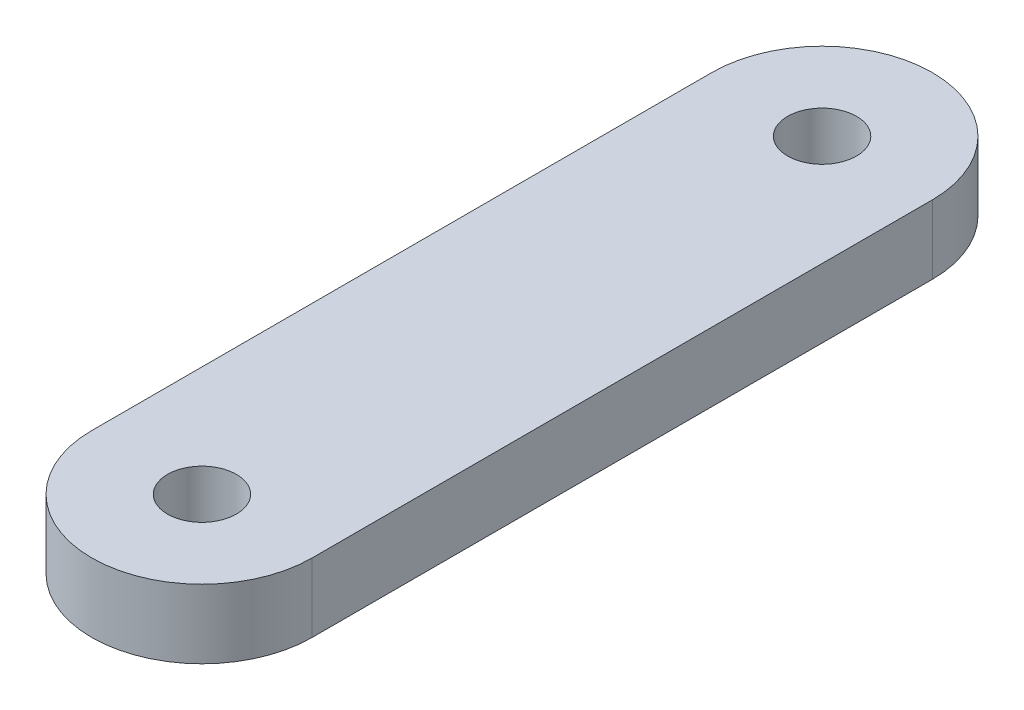
SolidWorks part; units mm, degrees
ref_plane "Front Plane" through (0, 0, 0) normal (0, 0, 1) x (1, 0, 0)
ref_plane "Top Plane" through (0, 0, 0) normal (0, 1, 0) x (1, 0, 0)
ref_plane "Right Plane" through (0, 0, 0) normal (1, 0, 0) x (0, 0, -1)
sketch "Sketch1" plane through (0, 0, 0) normal (0, 1, 0) x (1, 0, 0)
  line L0 (0, 0) -> (0, 22.5) construction
  line L1 (-4, 0) -> (-4, 22.5)
  line L2 (4, 0) -> (4, 22.5)
  arc A0 (-4, 0) -> (4, 0) centre (0, 0) ccw
  arc A1 (4, 22.5) -> (-4, 22.5) centre (0, 22.5) ccw
  circle A2 centre (0, 22.5) radius 1.25
  circle A3 centre (0, 0) radius 1.25
  point P3 (0, 11.25)
  dimension "D2" = 4
  dimension "D3" = 2.5
  dimension "D1" = 22.5
extrude "Boss-Extrude1" add sketch "Sketch1" along normal blind 2.5
